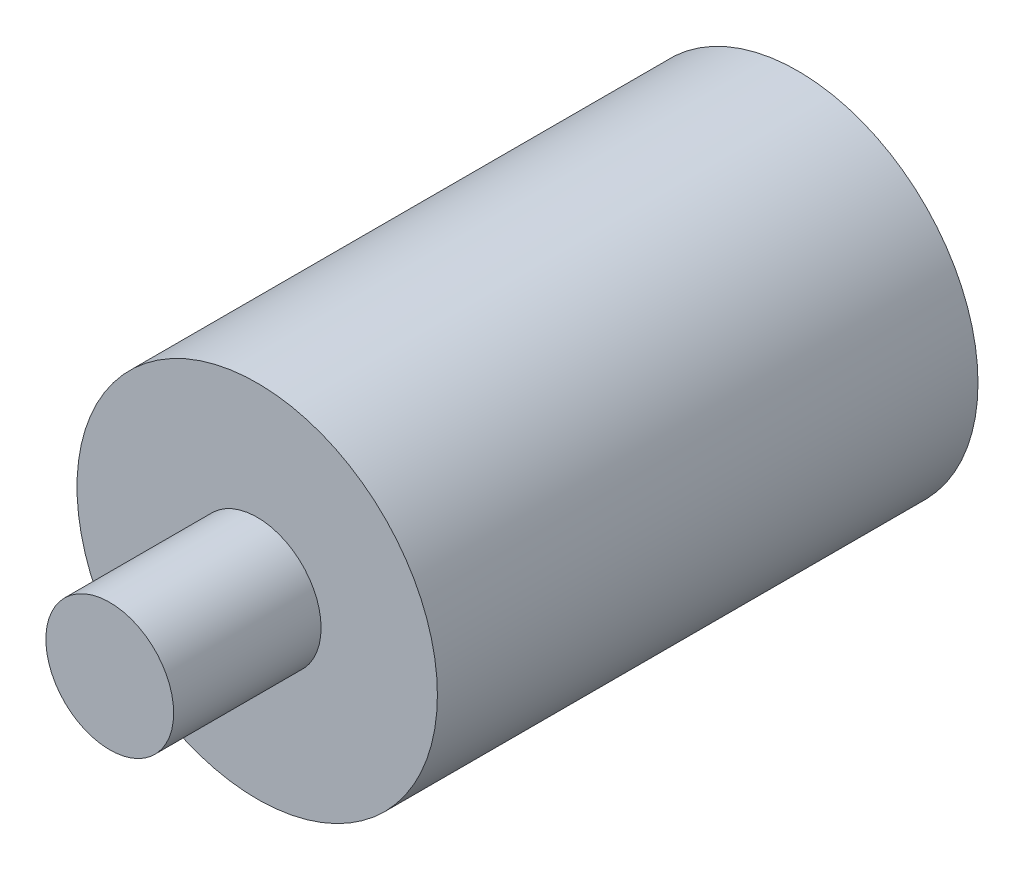
SolidWorks part; units mm, degrees
material "ABS"
ref_plane "Plan de face" through (0, 0, 0) normal (0, 0, 1) x (1, 0, 0)
ref_plane "Plan de dessus" through (0, 0, 0) normal (0, 1, 0) x (1, 0, 0)
ref_plane "Plan de droite" through (0, 0, 0) normal (1, 0, 0) x (0, 0, -1)
sketch "Esquisse1" plane through (0, 0, 0) normal (0, 0, 1) x (1, 0, 0)
  circle A0 centre (0, 0) radius 11
  dimension "D1" = 22
extrude "Boss.-Extru.1" add sketch "Esquisse1" along normal blind 33
sketch "Esquisse2" plane through (0, 0, 33) normal (0, 0, 1) x (1, 0, 0)
  circle A0 centre (0, 0) radius 3.9
  dimension "D1" = 7.8
extrude "Boss.-Extru.2" add sketch "Esquisse2" along normal blind 9
